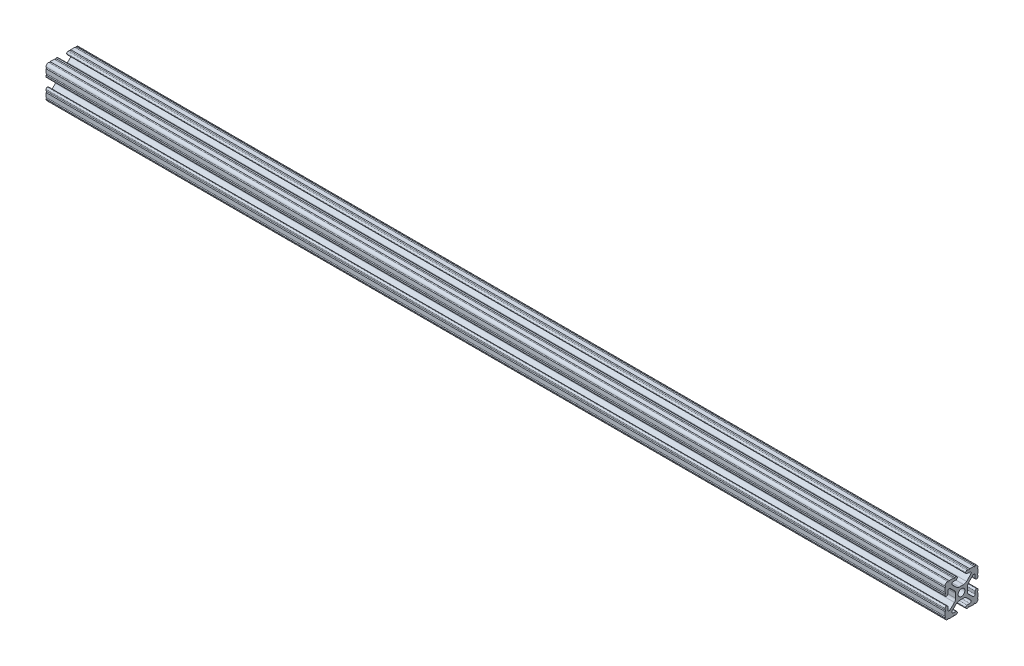
SolidWorks part; units mm, degrees
material "6061-T6 (SS)"
ref_plane "Front Plane" through (0, 0, 0) normal (0, 0, 1) x (1, 0, 0)
ref_plane "Top Plane" through (0, 0, 0) normal (0, 1, 0) x (1, 0, 0)
ref_plane "Right Plane" through (0, 0, 0) normal (1, 0, 0) x (0, 0, -1)
sketch "Sketch1" plane through (0, 0, 0) normal (1, 0, 0) x (0, 0, -1)
  line L0 (6.3331, -12.7) -> (9.5504, -12.7)
  line L1 (12.7, -9.5504) -> (12.7, -6.3331)
  line L2 (12.7, -5.3171) -> (12.7, -4.2875)
  line L3 (11.651, -3.2385) -> (11.5392, -3.2385)
  line L4 (10.4902, -4.2875) -> (10.4902, -6.4021)
  line L5 (8.7371, -7.1294) -> (5.441, -3.8408)
  line L6 (4.5085, -1.5932) -> (4.5085, 1.5932)
  line L7 (5.441, 3.8408) -> (8.7371, 7.1294)
  line L8 (10.4902, 6.4021) -> (10.4902, 4.2875)
  line L9 (11.5392, 3.2385) -> (11.651, 3.2385)
  line L10 (12.7, 4.2875) -> (12.7, 5.3171)
  line L11 (12.7, 6.3331) -> (12.7, 9.5504)
  line L12 (9.5504, 12.7) -> (6.3331, 12.7)
  line L13 (5.3171, 12.7) -> (4.2875, 12.7)
  line L14 (3.2385, 11.651) -> (3.2385, 11.5392)
  line L15 (4.2875, 10.4902) -> (6.4768, 10.4902)
  line L16 (7.207, 8.7244) -> (3.8983, 5.4232)
  line L17 (1.6558, 4.4958) -> (-1.6558, 4.4958)
  line L18 (-3.8983, 5.4232) -> (-7.207, 8.7244)
  line L19 (-6.4768, 10.4902) -> (-4.2875, 10.4902)
  line L20 (-3.2385, 11.5392) -> (-3.2385, 11.651)
  line L21 (-4.2875, 12.7) -> (-5.3171, 12.7)
  line L22 (-6.3331, 12.7) -> (-9.5504, 12.7)
  line L23 (-12.7, 9.5504) -> (-12.7, 6.3331)
  line L24 (-12.7, 5.3171) -> (-12.7, 4.2875)
  line L25 (-11.651, 3.2385) -> (-11.5392, 3.2385)
  line L26 (-10.4902, 4.2875) -> (-10.4902, 6.4021)
  line L27 (-8.7371, 7.1294) -> (-5.441, 3.8408)
  line L28 (-4.5085, 1.5932) -> (-4.5085, -1.5932)
  line L29 (-5.441, -3.8408) -> (-8.7371, -7.1294)
  line L30 (-10.4902, -6.4021) -> (-10.4902, -4.2875)
  line L31 (-11.5392, -3.2385) -> (-11.651, -3.2385)
  line L32 (-12.7, -4.2875) -> (-12.7, -5.3171)
  line L33 (-12.7, -6.3331) -> (-12.7, -9.5504)
  line L34 (-9.5504, -12.7) -> (-6.3331, -12.7)
  line L35 (-5.3171, -12.7) -> (-4.2875, -12.7)
  line L36 (-3.2385, -11.651) -> (-3.2385, -11.5392)
  line L37 (-4.2875, -10.4902) -> (-6.4164, -10.4902)
  line L38 (-7.1797, -8.6452) -> (-3.9523, -5.4237)
  line L39 (-1.7093, -4.4958) -> (1.7093, -4.4958)
  line L40 (3.9523, -5.4237) -> (7.1797, -8.6452)
  line L41 (6.4164, -10.4902) -> (4.2875, -10.4902)
  line L42 (3.2385, -11.5392) -> (3.2385, -11.651)
  line L43 (4.2875, -12.7) -> (5.3171, -12.7)
  circle A0 centre (0, 0) radius 2.6035
  arc A1 (6.3331, -12.7) -> (5.3171, -12.7) centre (5.8251, -12.7) ccw
  arc A2 (10.5664, -12.6998) -> (9.5504, -12.7) centre (10.0584, -12.7) ccw
  arc A3 (10.5664, -12.6998) -> (12.6998, -10.5664) centre (10.5918, -10.5918) ccw
  arc A4 (12.7, -9.5504) -> (12.6998, -10.5664) centre (12.7, -10.0584) ccw
  arc A5 (12.7, -5.3171) -> (12.7, -6.3331) centre (12.7, -5.8251) ccw
  arc A6 (12.7, -4.2875) -> (11.651, -3.2385) centre (11.651, -4.2875) ccw
  arc A7 (11.5392, -3.2385) -> (10.4902, -4.2875) centre (11.5392, -4.2875) ccw
  arc A8 (8.7371, -7.1294) -> (10.4902, -6.4021) centre (9.4628, -6.4021) ccw
  arc A9 (5.441, 3.8408) -> (4.5085, 1.5932) centre (7.6835, 1.5932) ccw
  arc A10 (10.4902, 6.4021) -> (8.7371, 7.1294) centre (9.4628, 6.4021) ccw
  arc A11 (10.4902, 4.2875) -> (11.5392, 3.2385) centre (11.5392, 4.2875) ccw
  arc A12 (11.651, 3.2385) -> (12.7, 4.2875) centre (11.651, 4.2875) ccw
  arc A13 (12.7, 6.3331) -> (12.7, 5.3171) centre (12.7, 5.8251) ccw
  arc A14 (12.6998, 10.5664) -> (12.7, 9.5504) centre (12.7, 10.0584) ccw
  arc A15 (12.6998, 10.5664) -> (10.5664, 12.6998) centre (10.5918, 10.5918) ccw
  arc A16 (9.5504, 12.7) -> (10.5664, 12.6998) centre (10.0584, 12.7) ccw
  arc A17 (5.3171, 12.7) -> (6.3331, 12.7) centre (5.8251, 12.7) ccw
  arc A18 (4.2875, 12.7) -> (3.2385, 11.651) centre (4.2875, 11.651) ccw
  arc A19 (3.2385, 11.5392) -> (4.2875, 10.4902) centre (4.2875, 11.5392) ccw
  arc A20 (7.207, 8.7244) -> (6.4768, 10.4902) centre (6.4768, 9.4563) ccw
  arc A21 (1.6558, 4.4958) -> (3.8983, 5.4232) centre (1.6558, 7.6708) ccw
  arc A22 (-3.8983, 5.4232) -> (-1.6558, 4.4958) centre (-1.6558, 7.6708) ccw
  arc A23 (-6.4768, 10.4902) -> (-7.207, 8.7244) centre (-6.4768, 9.4563) ccw
  arc A24 (-4.2875, 10.4902) -> (-3.2385, 11.5392) centre (-4.2875, 11.5392) ccw
  arc A25 (-3.2385, 11.651) -> (-4.2875, 12.7) centre (-4.2875, 11.651) ccw
  arc A26 (-6.3331, 12.7) -> (-5.3171, 12.7) centre (-5.8251, 12.7) ccw
  arc A27 (-10.5664, 12.6998) -> (-9.5504, 12.7) centre (-10.0584, 12.7) ccw
  arc A28 (-10.5664, 12.6998) -> (-12.6998, 10.5664) centre (-10.5918, 10.5918) ccw
  arc A29 (-12.7, 9.5504) -> (-12.6998, 10.5664) centre (-12.7, 10.0584) ccw
  arc A30 (-12.7, 5.3171) -> (-12.7, 6.3331) centre (-12.7, 5.8251) ccw
  arc A31 (-12.7, 4.2875) -> (-11.651, 3.2385) centre (-11.651, 4.2875) ccw
  arc A32 (-11.5392, 3.2385) -> (-10.4902, 4.2875) centre (-11.5392, 4.2875) ccw
  arc A33 (-8.7371, 7.1294) -> (-10.4902, 6.4021) centre (-9.4628, 6.4021) ccw
  arc A34 (-4.5085, 1.5932) -> (-5.441, 3.8408) centre (-7.6835, 1.5932) ccw
  arc A35 (-5.441, -3.8408) -> (-4.5085, -1.5932) centre (-7.6835, -1.5932) ccw
  arc A36 (-10.4902, -6.4021) -> (-8.7371, -7.1294) centre (-9.4628, -6.4021) ccw
  arc A37 (-10.4902, -4.2875) -> (-11.5392, -3.2385) centre (-11.5392, -4.2875) ccw
  arc A38 (-11.651, -3.2385) -> (-12.7, -4.2875) centre (-11.651, -4.2875) ccw
  arc A39 (-12.7, -6.3331) -> (-12.7, -5.3171) centre (-12.7, -5.8251) ccw
  arc A40 (-12.6998, -10.5664) -> (-12.7, -9.5504) centre (-12.7, -10.0584) ccw
  arc A41 (-12.6998, -10.5664) -> (-10.5664, -12.6998) centre (-10.5918, -10.5918) ccw
  arc A42 (-9.5504, -12.7) -> (-10.5664, -12.6998) centre (-10.0584, -12.7) ccw
  arc A43 (-5.3171, -12.7) -> (-6.3331, -12.7) centre (-5.8251, -12.7) ccw
  arc A44 (-4.2875, -12.7) -> (-3.2385, -11.651) centre (-4.2875, -11.651) ccw
  arc A45 (-3.2385, -11.5392) -> (-4.2875, -10.4902) centre (-4.2875, -11.5392) ccw
  arc A46 (-7.1797, -8.6452) -> (-6.4164, -10.4902) centre (-6.4164, -9.4098) ccw
  arc A47 (-1.7093, -4.4958) -> (-3.9523, -5.4237) centre (-1.7093, -7.6708) ccw
  arc A48 (3.9523, -5.4237) -> (1.7093, -4.4958) centre (1.7093, -7.6708) ccw
  arc A49 (6.4164, -10.4902) -> (7.1797, -8.6452) centre (6.4164, -9.4098) ccw
  arc A50 (4.2875, -10.4902) -> (3.2385, -11.5392) centre (4.2875, -11.5392) ccw
  arc A51 (3.2385, -11.651) -> (4.2875, -12.7) centre (4.2875, -11.651) ccw
  arc A52 (5.441, -3.8408) -> (4.5085, -1.5932) centre (7.6835, -1.5932) cw
  dimension "D1" = 3.175
extrude "Boss-Extrude1" add sketch "Sketch1" along normal mid plane 692.15
